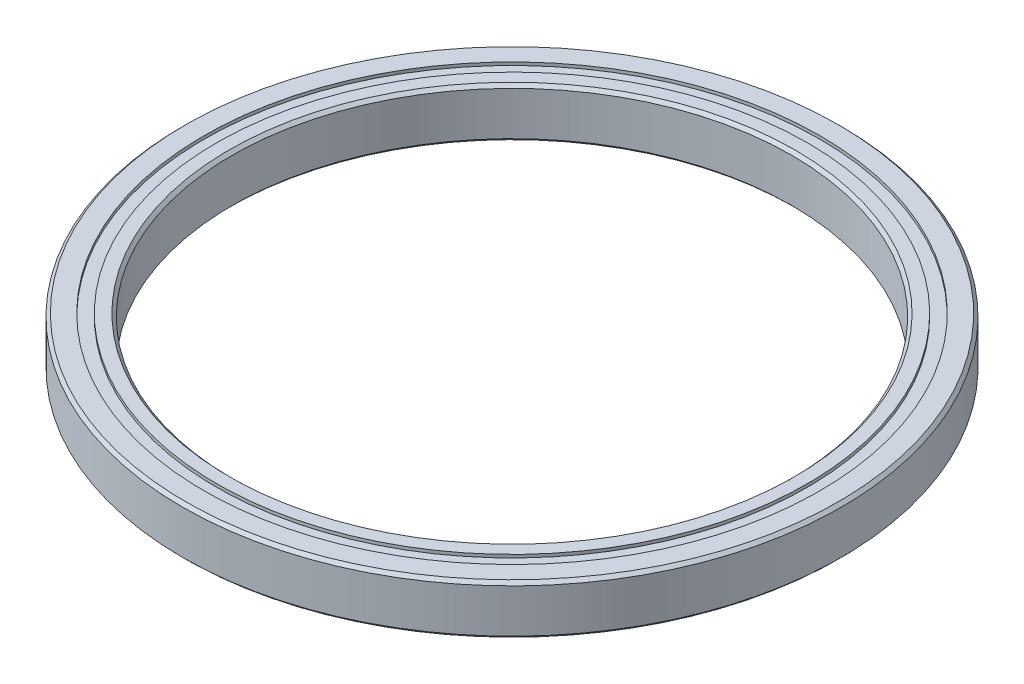
SolidWorks part; units mm, degrees
material "AISI 304"
ref_plane "前视基准面" through (0, 0, 0) normal (0, 0, 1) x (1, 0, 0)
ref_plane "上视基准面" through (0, 0, 0) normal (0, 1, 0) x (1, 0, 0)
ref_plane "右视基准面" through (0, 0, 0) normal (1, 0, 0) x (0, 0, -1)
sketch "草图1" plane through (0, 0, 0) normal (0, 0, 1) x (1, 0, 0)
  line L0 (0, 0) -> (0, 30) construction
  line L1 (-45.5, 0) -> (-47.5, 0)
  line L2 (-53, 0.5) -> (-53, 7.5)
  line L3 (-52.5, 8) -> (-49.5, 8)
  line L4 (-45, 7.5) -> (-45, 0.5)
  line L5 (-49.5, 8) -> (-49.5, 7.5)
  line L6 (-49.5, 7.5) -> (-47.5, 7.5)
  line L7 (-47.5, 7.5) -> (-47.5, 8)
  line L8 (-49.5, 0) -> (-49.5, 0.5)
  line L9 (-49.5, 0.5) -> (-47.5, 0.5)
  line L10 (-47.5, 0.5) -> (-47.5, 0)
  line L11 (-47.5, 8) -> (-45.5, 8)
  line L12 (-49.5, 0) -> (-52.5, 0)
  line L13 (-53, 7.5) -> (-52.5, 8)
  line L14 (-52.5, 0) -> (-53, 0.5)
  line L15 (-45.5, 8) -> (-45, 7.5)
  line L16 (-45, 0.5) -> (-45.5, 0)
  point P3 (-45, 0)
  point P4 (-53, 0)
  point P5 (-53, 8)
  point P7 (-45, 8)
  point P13 (-48.5, 0.5)
  dimension "D1" = 30
  dimension "D2" = 8
  dimension "D3" = 90
  dimension "D4" = 106
  dimension "D5" = 0.5
  dimension "D6" = 97
  dimension "D7" = 2
revolve "旋转1" add sketch "草图1" angle 360 about L0
